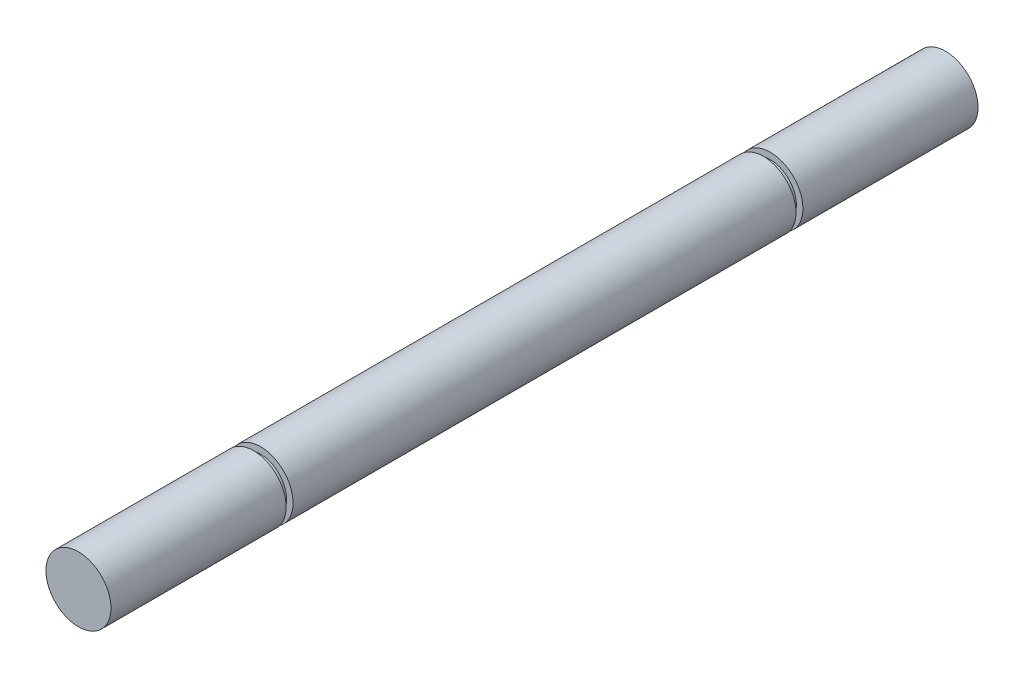
SolidWorks part; units mm, degrees
ref_plane "Front Plane" through (0, 0, 0) normal (0, 0, 1) x (1, 0, 0)
ref_plane "Top Plane" through (0, 0, 0) normal (0, 1, 0) x (1, 0, 0)
ref_plane "Right Plane" through (0, 0, 0) normal (1, 0, 0) x (0, 0, -1)
sketch "Sketch1" plane through (0, 0, 0) normal (0, 0, 1) x (1, 0, 0)
  circle A0 centre (0, 0) radius 4.7625
  dimension "D1" = 9.525
extrude "Boss-Extrude1" add sketch "Sketch1" along normal blind 73.66
sketch "Sketch2" plane through (0, 0, 0) normal (0, 0, -1) x (-1, 0, 0)
  circle A0 centre (0, 0) radius 3.81
  dimension "D1" = 7.62
extrude "Boss-Extrude2" add sketch "Sketch2" along normal blind 1.016
sketch "Sketch3" plane through (0, 0, -1.016) normal (0, 0, -1) x (-1, 0, 0)
  circle A0 centre (0, 0) radius 4.7625
  dimension "D1" = 9.525
extrude "Boss-Extrude3" add sketch "Sketch3" along normal blind 25.654
sketch "Sketch4" plane through (0, 0, 73.66) normal (0, 0, 1) x (1, 0, 0)
  circle A0 centre (0, 0) radius 3.81
  dimension "D1" = 7.62
extrude "Boss-Extrude4" add sketch "Sketch4" along normal blind 1.016
sketch "Sketch5" plane through (0, 0, 74.676) normal (0, 0, 1) x (1, 0, 0)
  circle A0 centre (0, 0) radius 4.7625
  dimension "D1" = 9.525
extrude "Boss-Extrude5" add sketch "Sketch5" along normal blind 25.654
